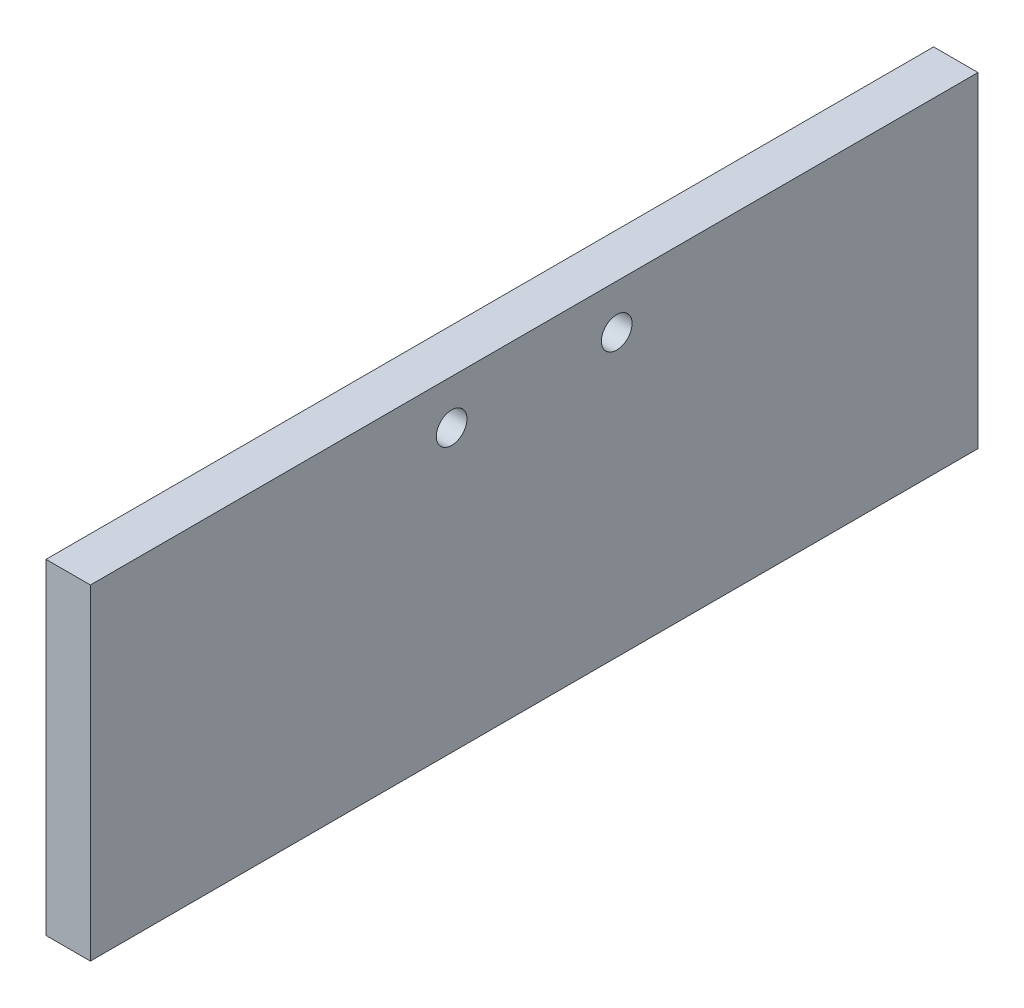
SolidWorks part; units mm, degrees
ref_plane "Front Plane" through (0, 0, 0) normal (0, 0, 1) x (1, 0, 0)
ref_plane "Top Plane" through (0, 0, 0) normal (0, 1, 0) x (1, 0, 0)
ref_plane "Right Plane" through (0, 0, 0) normal (1, 0, 0) x (0, 0, -1)
sketch "Sketch1" plane through (0, 0, 0) normal (1, 0, 0) x (0, 0, -1)
  line L0 (-63.5, 0) -> (63.5, 0) construction
  line L1 (-63.5, 6.35) -> (63.5, 6.35)
  line L2 (-63.5, 6.35) -> (-63.5, -6.35)
  line L3 (-63.5, -6.35) -> (63.5, -6.35)
  line L4 (63.5, 6.35) -> (63.5, -6.35)
  line L5 (-63.5, 6.35) -> (63.5, -6.35) construction
  line L6 (-63.5, -6.35) -> (63.5, 6.35) construction
  line L8 (-63.5, -6.35) -> (63.5, -6.35)
  line L9 (-63.5, -6.35) -> (-63.5, -40.259)
  line L10 (-63.5, -40.259) -> (63.5, -40.259)
  line L11 (63.5, -6.35) -> (63.5, -40.259)
  circle A0 centre (-11.811, 0) radius 2.1971
  circle A1 centre (11.811, 0) radius 2.1971
  point P0 (0, 0)
  dimension "D5" = 4.3942
  dimension "D6" = 4.3942
  dimension "D1" = 127
  dimension "D2" = 12.7
  dimension "D3" = 11.811
  dimension "D4" = 11.811
  dimension "D7" = 33.909
extrude "Boss-Extrude1" add sketch "Sketch1" along normal blind 6.35 contours L4 L1 L2 L3 A1 A0 | L11 L3 L9 L10
